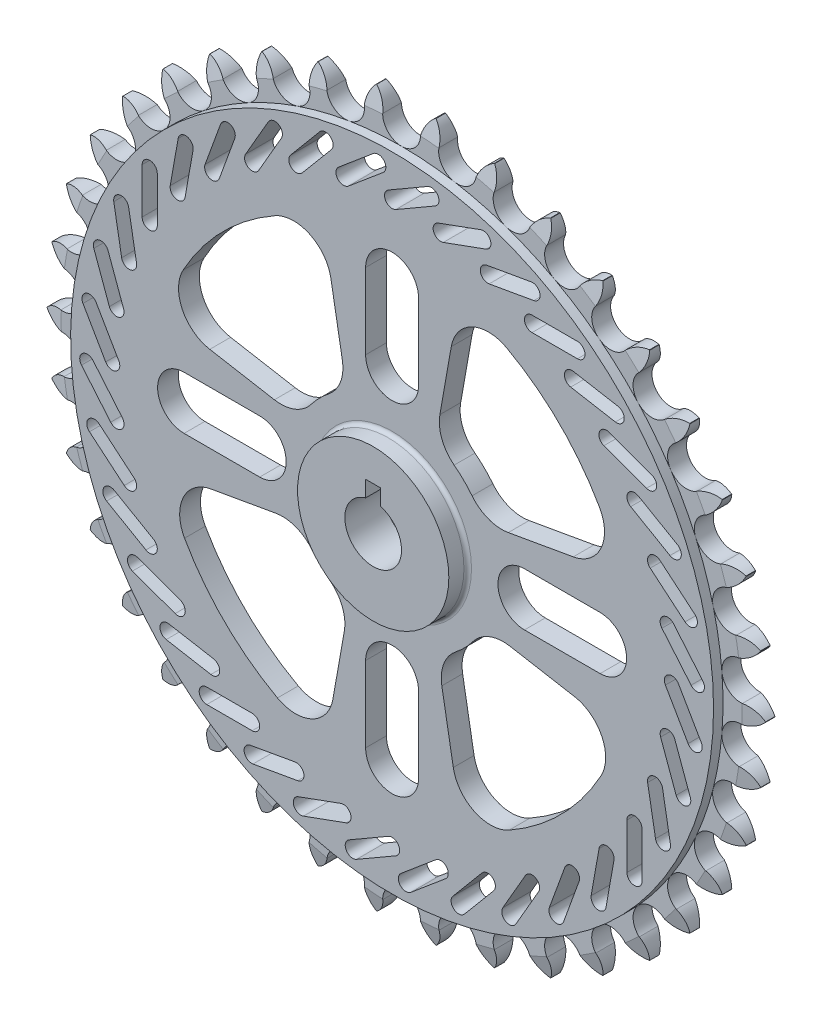
SolidWorks part; units mm, degrees
material "AISI 1045 Steel, cold drawn"
ref_plane "Front Plane" through (0, 0, 0) normal (0, 0, 1) x (1, 0, 0)
ref_plane "Top Plane" through (0, 0, 0) normal (0, 1, 0) x (1, 0, 0)
ref_plane "Right Plane" through (0, 0, 0) normal (1, 0, 0) x (0, 0, -1)
sketch "Sketch1" plane through (0, 0, 0) normal (0, 0, 1) x (1, 0, 0)
  circle A0 centre (0, 0) radius 95
  dimension "D1" = 190
extrude "Boss-Extrude1" add sketch "Sketch1" along normal mid plane 5
sketch "Sketch2" plane through (0, 0, 2.5) normal (0, 0, 1) x (1, 0, 0)
  circle A0 centre (0, 0) radius 85
  dimension "D1" = 170
extrude "Boss-Extrude2" add sketch "Sketch2" along normal blind 2.5
sketch "Sketch4" plane through (0, 0, 0) normal (1, 0, 0) x (0, 0, -1)
  line L0 (0, 0) -> (0, 108.584) construction
  line L1 (-2.5, 90) -> (2.5, 90) construction
  line L2 (-2.5, 95) -> (-2.5, -95) construction
  line L3 (2.5, -95) -> (2.5, 95) construction
  line L4 (-2.5, 90) -> (0, 100)
  line L5 (0, 100) -> (2.5, 90)
  line L6 (-2.5, 90) -> (-7.5, 90)
  line L7 (-7.5, 90) -> (-7.5, 105)
  line L8 (-7.5, 105) -> (7.5, 105)
  line L9 (7.5, 105) -> (7.5, 90)
  line L10 (7.5, 90) -> (2.5, 90)
  line L11 (0, 0) -> (41.762, 0) construction
  dimension "D1" = 90
  dimension "D2" = 10
  dimension "D3" = 5
  dimension "D4" = 5
  dimension "D5" = 15
revolve "Cut-Revolve1" cut sketch "Sketch4" angle 360 about L11
sketch "Sketch5" plane through (0, 0, 5) normal (0, 0, 1) x (1, 0, 0)
  line L0 (0, 0) -> (0, 95) construction
  circle A0 centre (0, 0) radius 95 construction
  circle A1 centre (0, 90) radius 5
  circle A2 centre (0, 0) radius 90 construction
  circle A3 centre (0, 0) radius 85 construction
  arc A4 (-5, 90) -> (-7.7979, 94.6794) centre (-12.1069, 88.9269) ccw
  arc A5 (5, 90) -> (7.7979, 94.6794) centre (12.1069, 88.9269) cw
  dimension "D2" = 7.1874
  dimension "D1" = 7.7979
sketch "Sketch6" plane through (0, 0, 5) normal (0, 0, 1) x (1, 0, 0)
  arc A0 (-5, 90) -> (-7.7979, 94.6794) centre (-12.1069, 88.9269) ccw construction
  circle A1 centre (0, 90) radius 5 construction
  arc A2 (7.7979, 94.6794) -> (5, 90) centre (12.1069, 88.9269) ccw construction
  arc A3 (7.7979, 94.6794) -> (5, 90) centre (12.1069, 88.9269) ccw
  arc A4 (-5, 90) -> (5, 90) centre (0, 90) ccw
  arc A5 (-5, 90) -> (-7.7979, 94.6794) centre (-12.1069, 88.9269) ccw
  arc A6 (-7.7979, 94.6794) -> (7.7979, 94.6794) centre (0, 86.8816) cw
  dimension "D1" = 11.0278
extrude "Cut-Extrude1" cut sketch "Sketch6" against normal through all
pattern_circular "CirPattern1" count 38 over 360 about axis through (0, 0, 0) along (0, 0, 1) of "Cut-Extrude1"
sketch "Sketch7" plane through (0, 0, 5) normal (0, 0, 1) x (1, 0, 0)
  line L0 (0, 74) -> (10.3923, 80) construction
  line L1 (0, 0) -> (0, 95) construction
  line L2 (-1, 75.7321) -> (9.3923, 81.7321)
  line L3 (1, 72.2679) -> (11.3923, 78.2679)
  circle A0 centre (0, 0) radius 7.5
  circle A1 centre (0, 0) radius 20
  circle A2 centre (0, 0) radius 70
  arc A3 (-1, 75.7321) -> (1, 72.2679) centre (0, 74) ccw
  arc A4 (11.3923, 78.2679) -> (9.3923, 81.7321) centre (10.3923, 80) ccw
  point P9 (5.1962, 77)
  dimension "D1" = 15
  dimension "D2" = 40
  dimension "D3" = 140
  dimension "D7" = 74
  dimension "D4" = 12
  dimension "D5" = 2
  dimension "D6" = 120
extrude "Cut-Extrude2" cut sketch "Sketch7" against normal through all
pattern_circular "CirPattern2" count 36 over 360 about axis through (0, 0, 0) along (0, 0, 1) of "Cut-Extrude2"
sketch "Sketch8" plane through (0, 0, 5) normal (0, 0, 1) x (1, 0, 0)
  line L0 (0, 55) -> (0, 35) construction
  line L1 (0, 0) -> (0, 95) construction
  line L2 (7, 55) -> (7, 35)
  line L3 (-7, 55) -> (-7, 35)
  circle A0 centre (0, 0) radius 70 construction
  circle A1 centre (0, 0) radius 70 construction
  arc A2 (7, 55) -> (-7, 55) centre (0, 55) ccw
  arc A3 (-7, 35) -> (7, 35) centre (0, 35) ccw
  point P7 (0, 45)
  dimension "D1" = 20
  dimension "D2" = 35
  dimension "D3" = 7
extrude "Cut-Extrude3" cut sketch "Sketch8" against normal through all
pattern_circular "CirPattern3" count 4 over 360 about axis through (0, 0, 0) along (0, 0, 1) of "Cut-Extrude3"
sketch "Sketch9" plane through (0, 0, 5) normal (0, 0, 1) x (1, 0, 0)
  line L0 (-48.1998, 15.6501) -> (-31.1194, 12.6384)
  line L1 (-16.182, 47.904) -> (-13.1519, 30.7193)
  line L2 (-7, 55) -> (-7, 35) construction
  line L3 (0, 0) -> (0, 95) construction
  line L4 (-35, 7) -> (-55, 7) construction
  circle A2 centre (0, 0) radius 63
  circle A3 centre (0, 0) radius 63 construction
  arc A4 (-55.23, 30.3092) -> (-30.9414, 54.8783) centre (0, 0) cw
  circle A5 centre (0, 0) radius 27
  circle A6 centre (0, 0) radius 27 construction
  arc A7 (-21.4416, 16.4091) -> (-16.7837, 21.1496) centre (0, 0) cw
  arc A8 (-35, -7) -> (-35, 7) centre (-35, 0) ccw construction
  arc A9 (-13.1519, 30.7193) -> (-16.7837, 21.1496) centre (-22.9999, 28.9828) cw
  arc A10 (-31.1194, 12.6384) -> (-21.4416, 16.4091) centre (-29.383, 22.4865) ccw
  arc A11 (-16.182, 47.904) -> (-30.9414, 54.8783) centre (-26.0301, 46.1675) ccw
  arc A12 (-48.1998, 15.6501) -> (-55.23, 30.3092) centre (-46.4633, 25.4982) cw
  point P21 (-28, 0)
  point P24 (-12, 24.1868)
  point P27 (-24.4464, 11.4618)
  point P30 (-18.3615, 60.2649)
  point P33 (-60.4311, 17.8068)
  dimension "D7" = 10
  dimension "D3" = 10
  dimension "D4" = 12
  dimension "D5" = 10
  dimension "D6" = 12
  dimension "D1" = 7
  dimension "D2" = 7
extrude "Cut-Extrude4" cut sketch "Sketch9" against normal through all
pattern_circular "CirPattern4" count 4 over 360 about axis through (0, 0, 0) along (0, 0, 1) of "Cut-Extrude4"
sketch "Sketch10" plane through (0, 0, 0) normal (0, 0, 1) x (1, 0, 0)
  circle A0 centre (0, 0) radius 7.5 construction
  circle A1 centre (0, 0) radius 7.5
extrude "Cut-Extrude5" cut sketch "Sketch10" against normal through all both and the other way through all
sketch "Sketch11" plane through (0, 0, 0) normal (0, 0, 1) x (1, 0, 0)
  circle A0 centre (0, 0) radius 20 construction
  circle A1 centre (0, 0) radius 20
  circle A2 centre (0, 0) radius 7.5 construction
  circle A3 centre (0, 0) radius 7.5
extrude "Boss-Extrude3" add sketch "Sketch11" along normal blind 10
fillet "Fillet1" radius 1 1 edges at (20, 0, 5)
sketch "Sketch12" plane through (0, 0, 10) normal (0, 0, 1) x (1, 0, 0)
  line L0 (0, 0) -> (0, 95) construction
  line L1 (-2, 11.5) -> (2, 11.5)
  line L2 (-2, 11.5) -> (-2, 3.5)
  line L3 (-2, 3.5) -> (2, 3.5)
  line L4 (2, 11.5) -> (2, 3.5)
  line L5 (-2, 11.5) -> (2, 3.5) construction
  line L6 (-2, 3.5) -> (2, 11.5) construction
  point P0 (0, 7.5)
  dimension "D1" = 4
  dimension "D2" = 4
  dimension "D3" = 7.5
extrude "Cut-Extrude6" cut sketch "Sketch12" against normal through all both and the other way through all
ref_plane "Plane1" through (0, 0, -2.5) normal (0, 0, -1) x (-1, 0, 0)
sketch "Sketch14" plane through (0, 0, -2.5) normal (0, 0, -1) x (-1, 0, 0)
  circle A0 centre (0, 0) radius 70
  dimension "D1" = 140
extrude "Cut-Extrude7" cut sketch "Sketch14" against normal blind 2
fillet "Fillet2" radius 1 1 edges at (-70, 0, -0.5)
